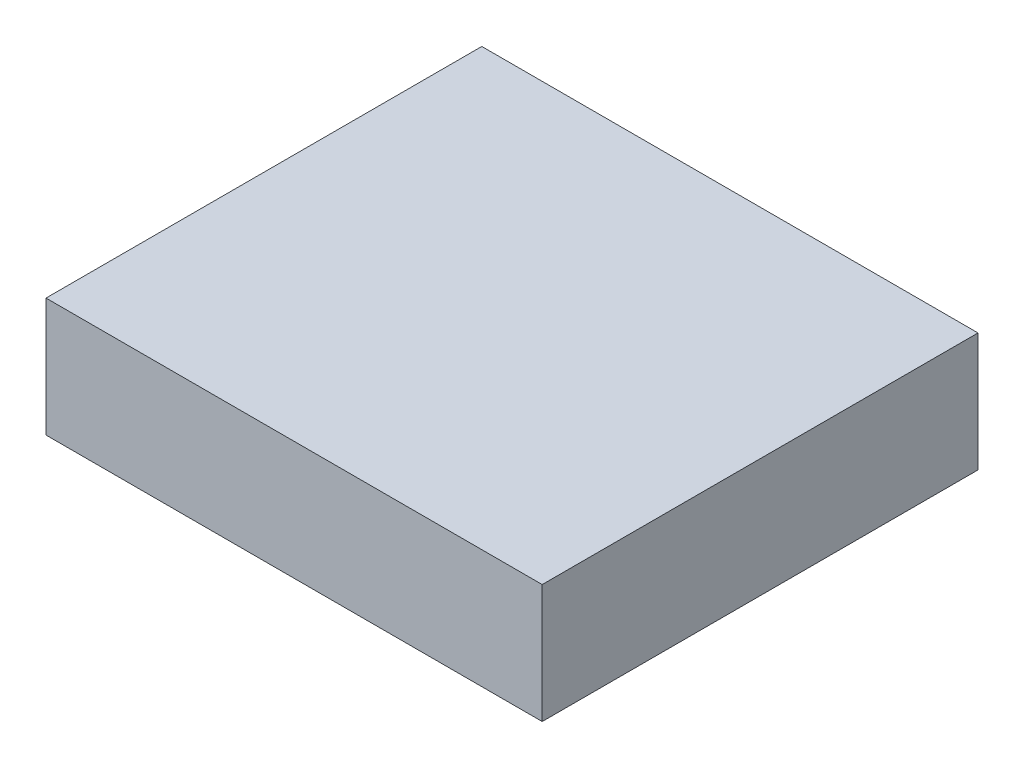
SolidWorks part; units mm, degrees
ref_plane "Front Plane" through (0, 0, 0) normal (0, 0, 1) x (1, 0, 0)
ref_plane "Top Plane" through (0, 0, 0) normal (0, 1, 0) x (1, 0, 0)
ref_plane "Right Plane" through (0, 0, 0) normal (1, 0, 0) x (0, 0, -1)
sketch "Sketch1" plane through (0, 0, 0) normal (0, 1, 0) x (1, 0, 0)
  line L1 (-57.5, -50.5) -> (57.5, -50.5)
  line L2 (-57.5, -50.5) -> (-57.5, 50.5)
  line L3 (-57.5, 50.5) -> (57.5, 50.5)
  line L4 (57.5, -50.5) -> (57.5, 50.5)
  line L5 (-57.5, -50.5) -> (57.5, 50.5) construction
  line L6 (-57.5, 50.5) -> (57.5, -50.5) construction
  point P0 (0, 0)
  dimension "D1" = 101
  dimension "D2" = 115
extrude "Boss-Extrude1" add sketch "Sketch1" along normal blind 27.5
ref_plane "Plane1" through (0, 0, 0) normal (-1, 0, 0) x (0, 0, 1)
